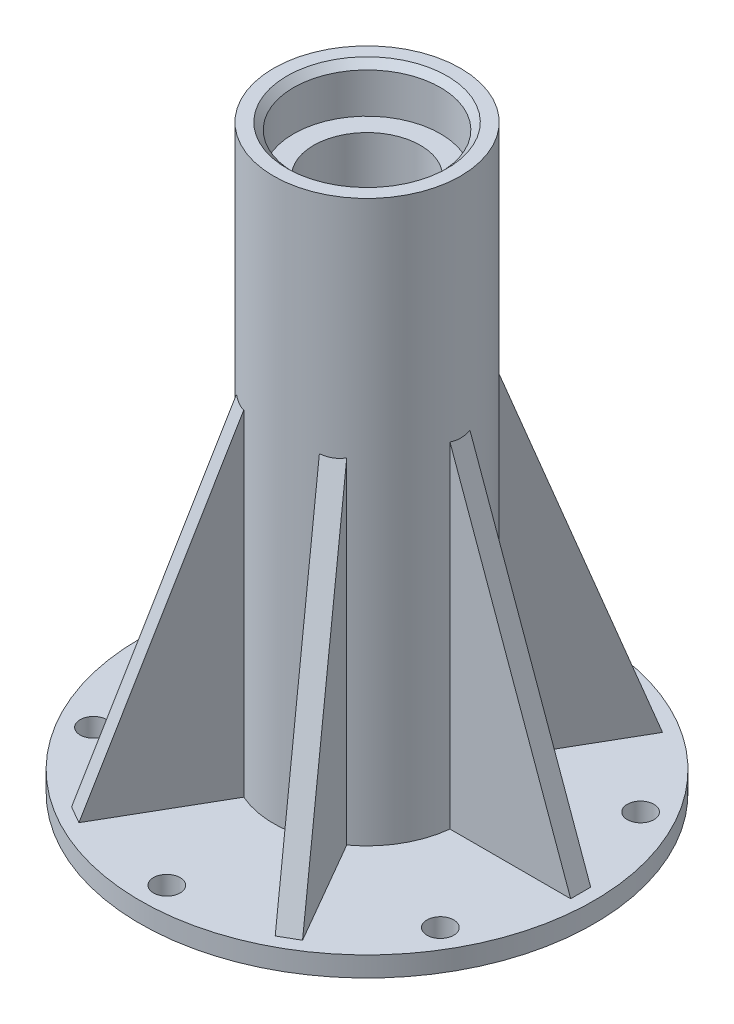
SolidWorks part; units mm, degrees
ref_plane "Plan de face" through (0, 0, 0) normal (0, 0, 1) x (1, 0, 0)
ref_plane "Plan de dessus" through (0, 0, 0) normal (0, 1, 0) x (1, 0, 0)
ref_plane "Plan de droite" through (0, 0, 0) normal (1, 0, 0) x (0, 0, -1)
sketch "Esquisse1" plane through (0, 0, 0) normal (0, 0, 1) x (1, 0, 0)
  line L0 (0, 5.7292) -> (0, -6.0347) construction
  line L1 (-8, 0) -> (-34, 0)
  line L2 (-34, 0) -> (-34, 3)
  line L3 (-34, 3) -> (-19, 3)
  line L4 (-14, 8) -> (-14, 87)
  line L5 (-14, 87) -> (-11, 87)
  line L6 (-11, 87) -> (-11, 80)
  line L7 (-11, 80) -> (-8, 80)
  line L8 (-8, 80) -> (-8, 0)
  line L9 (-19, 3) -> (-14, 3)
  line L10 (-14, 3) -> (-14, 8)
  point P13 (-14, 3)
  dimension "D1" = 11
  dimension "D2" = 3
  dimension "D3" = 3
  dimension "D4" = 20
  dimension "D5" = 3
  dimension "D6" = 7
  dimension "D7" = 84
revolve "Révolution1" add sketch "Esquisse1" angle 360 about L0
sketch "Esquisse2" plane through (0, 3, 0) normal (0, 1, 0) x (1, 0, 0)
  circle A0 centre (0, 30) radius 2
  circle A1 centre (25.9808, 15) radius 2
  circle A2 centre (25.9808, -15) radius 2
  circle A3 centre (0, -30) radius 2
  circle A4 centre (-25.9808, -15) radius 2
  circle A5 centre (-25.9808, 15) radius 2
  point P16 (0, 0)
  dimension "D1" = 4
  dimension "D2" = 30
  dimension "D3" = 6
extrude "Enlèv. mat.-Extru.1" cut sketch "Esquisse2" against normal through all
chamfer "Chanfrein1" distance 1 angle 45 1 edges at (-11, 87, 0)
sketch "Esquisse5" plane through (0, 0, 0) normal (0, 0, 1) x (1, 0, 0)
  line L0 (14, 53) -> (32, 3)
  line L3 (14, 3) -> (14, 87) construction
  line L4 (34, 3) -> (-34, 3) construction
  dimension "D1" = 2
  dimension "D2" = 50
rib "Nervure11" sketch "Esquisse5" sketch "Esquisse5" thickness 3 extrusion direction parallel to sketch draft on no parameters "D1"=3
pattern_circular "Répétition circulaire1" count 6 over 360 about axis through (0, 0, 0) along (0, 1, 0) of "Nervure11"
